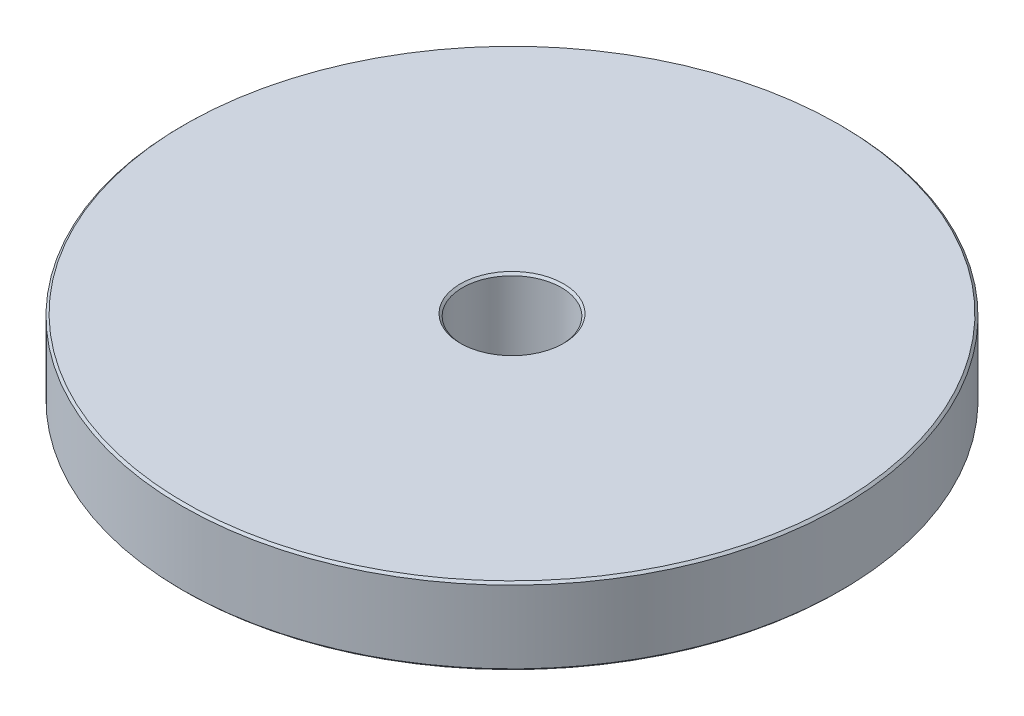
SolidWorks part; units mm, degrees
material "POM Acetal Copolymer"
ref_plane "Front Plane" through (0, 0, 0) normal (0, 0, 1) x (1, 0, 0)
ref_plane "Top Plane" through (0, 0, 0) normal (0, 1, 0) x (1, 0, 0)
ref_plane "Right Plane" through (0, 0, 0) normal (1, 0, 0) x (0, 0, -1)
sketch "Sketch1" plane through (0, 0, 0) normal (0, 0, 1) x (1, 0, 0)
  line L0 (4.7, -9.5) -> (29.8, -9.5)
  line L1 (29.8, -9.5) -> (30, -9.3)
  line L2 (30, -9.3) -> (30, -2.7)
  line L3 (4.7, -2.5) -> (29.8, -2.5)
  line L4 (4.5, -2.7) -> (4.7, -2.5)
  line L5 (29.8, -2.5) -> (30, -2.7)
  line L6 (4.5, -2.7) -> (4.5, -9.3)
  line L7 (4.5, -9.3) -> (4.7, -9.5)
  line L8 (0, 9.5) -> (0, -9.5) construction
  point P5 (30, -2.5)
  point P6 (4.5, -2.5)
  dimension "D1" = 9
  dimension "D2" = 60
  dimension "D4" = 7
  dimension "D5" = 9.5
  dimension "D7" = 0.2
  dimension "D8" = 0.2
revolve "Revolve1" add sketch "Sketch1" angle 360 about L8
